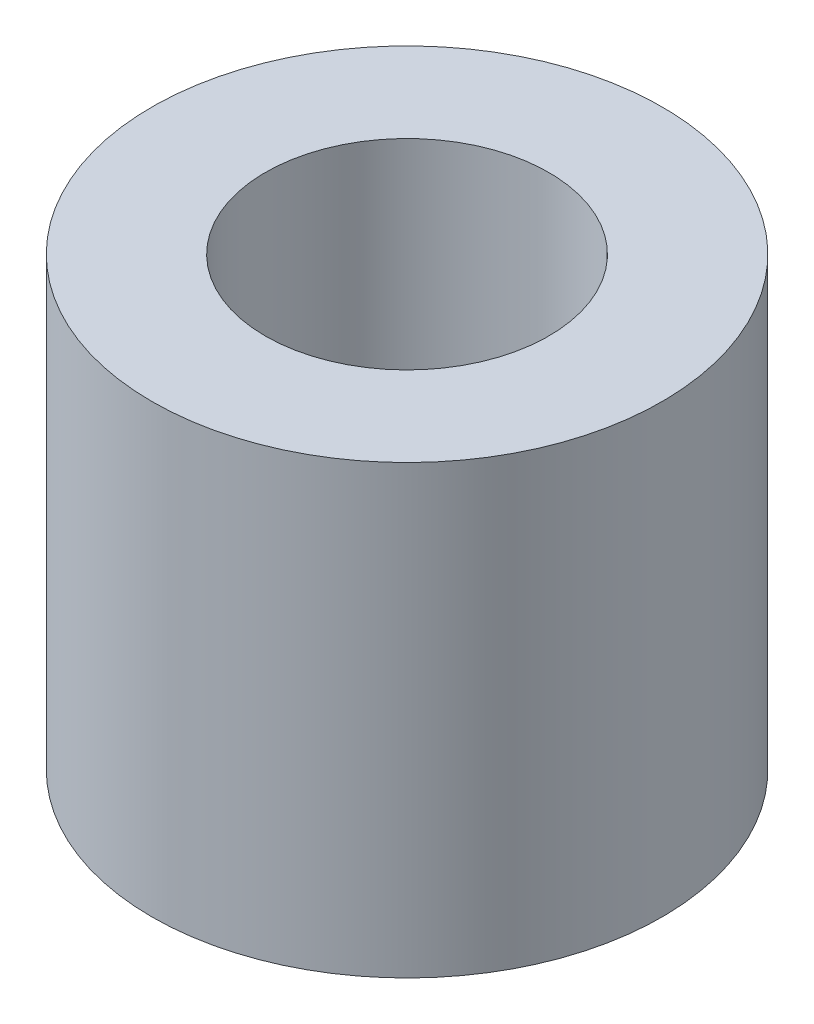
SolidWorks part; units mm, degrees
ref_plane "Front Plane" through (0, 0, 0) normal (0, 0, 1) x (1, 0, 0)
ref_plane "Top Plane" through (0, 0, 0) normal (0, 1, 0) x (1, 0, 0)
ref_plane "Right Plane" through (0, 0, 0) normal (1, 0, 0) x (0, 0, -1)
sketch "Sketch1" plane through (0, 0, 0) normal (0, 1, 0) x (1, 0, 0)
  circle A0 centre (0, 0) radius 3.175
  circle A1 centre (0, 0) radius 5.715
  dimension "D1" = 6.35
  dimension "D2" = 2.54
extrude "Boss-Extrude1" add sketch "Sketch1" along normal blind 10
